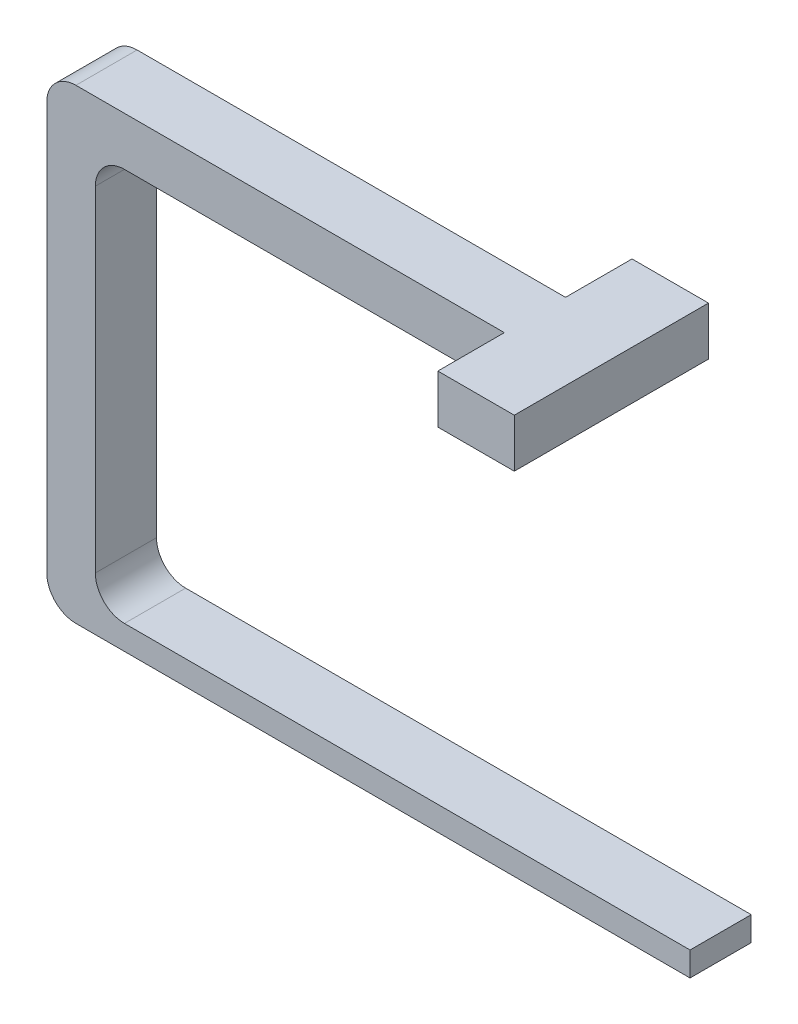
SolidWorks part; units mm, degrees
ref_plane "Front Plane" through (0, 0, 0) normal (0, 0, 1) x (1, 0, 0)
ref_plane "Top Plane" through (0, 0, 0) normal (0, 1, 0) x (1, 0, 0)
ref_plane "Right Plane" through (0, 0, 0) normal (1, 0, 0) x (0, 0, -1)
sketch "Sketch1" plane through (0, 0, 0) normal (0, 0, 1) x (1, 0, 0)
  line L1 (-28.575, 115.57) -> (-168.275, 115.57)
  line L2 (-28.575, 115.57) -> (-28.575, 102.87)
  line L3 (-28.575, 102.87) -> (-155.575, 102.87)
  line L4 (-168.275, 115.57) -> (-168.275, 102.87)
  line L6 (-168.275, 102.87) -> (-168.275, 0)
  line L8 (-155.575, 102.87) -> (-155.575, 0)
  line L9 (-155.575, 0) -> (0, 0)
  line L10 (-168.275, 0) -> (-168.275, -6.35)
  line L11 (-168.275, -6.35) -> (0, -6.35)
  line L12 (0, 0) -> (0, -6.35)
  point P10 (0, 0)
  point P12 (0, 0)
  point P13 (0, 0)
  dimension "D1" = 6.35
  dimension "D2" = 12.7
  dimension "D3" = 12.7
  dimension "D4" = 121.92
  dimension "D5" = 127
  dimension "D6" = 28.575
extrude "Boss-Extrude1" add sketch "Sketch1" along normal mid plane 16.002
sketch "Sketch2" plane through (0, 102.87, 0) normal (0, -1, 0) x (1, 0, 0)
  line L0 (-28.575, 8.001) -> (-28.575, -8.001) construction
  line L1 (-48.575, -25.4) -> (-28.575, -25.4)
  line L2 (-48.575, -25.4) -> (-48.575, 25.4)
  line L3 (-48.575, 25.4) -> (-28.575, 25.4)
  line L4 (-28.575, -25.4) -> (-28.575, 25.4)
  point P6 (-28.575, 0)
  dimension "D1" = 20
  dimension "D2" = 50.8
extrude "Boss-Extrude2" add sketch "Sketch2" against normal up to surface (12.7 mm away) up to face at (-98.425, 115.57, 0)
fillet "Fillet1" radius 7.62 4 edges at (-168.275, -6.35, 0) (-155.575, 0, 0) (-155.575, 102.87, 0) (-168.275, 115.57, 0)
